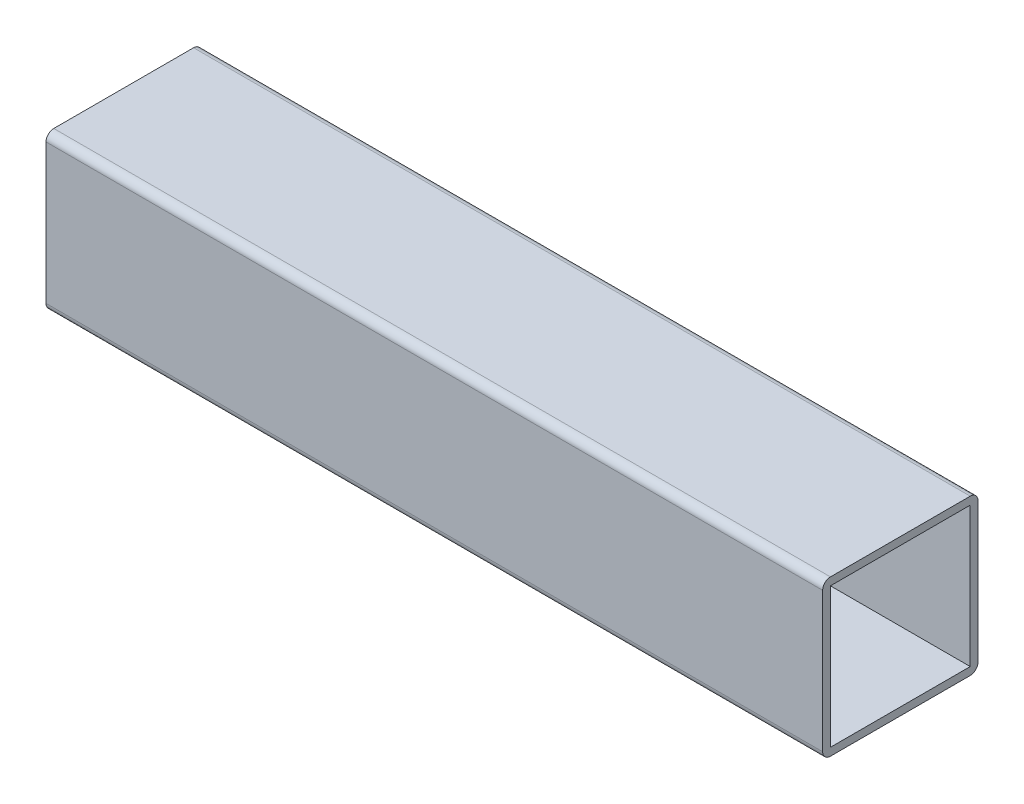
SolidWorks part; units mm, degrees
ref_plane "Спереди" through (0, 0, 0) normal (0, 0, 1) x (1, 0, 0)
ref_plane "Сверху" through (0, 0, 0) normal (0, 1, 0) x (1, 0, 0)
ref_plane "Справа" through (0, 0, 0) normal (1, 0, 0) x (0, 0, -1)
sketch "Эскиз1" plane through (0, 0, 0) normal (1, 0, 0) x (0, 0, -1)
  line L1 (-27, 30) -> (27, 30)
  line L2 (-30, 27) -> (-30, -27)
  line L3 (-27, -30) -> (27, -30)
  line L4 (30, 27) -> (30, -27)
  line L5 (-30, 30) -> (30, -30) construction
  line L6 (-30, -30) -> (30, 30) construction
  arc A0 (-30, -27) -> (-27, -30) centre (-27, -27) ccw
  arc A1 (27, -30) -> (30, -27) centre (27, -27) ccw
  arc A2 (27, 30) -> (30, 27) centre (27, 27) cw
  arc A3 (-27, 30) -> (-30, 27) centre (-27, 27) ccw
  point P0 (0, 0)
  dimension "D1" = 3
extrude "Вытянуть-Тонкостенный2" add sketch "Эскиз1" along normal blind 300 thin
